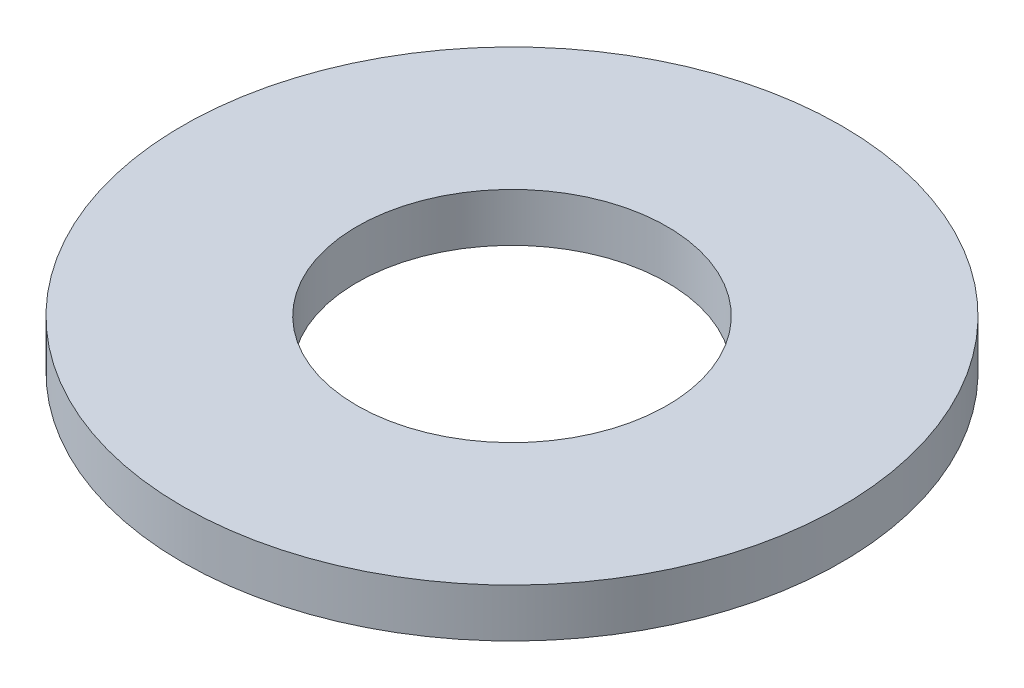
SolidWorks part; units mm, degrees
material "Cast Alloy Steel"
ref_plane "Front" through (0, 0, 0) normal (0, 0, 1) x (1, 0, 0)
ref_plane "Top" through (0, 0, 0) normal (0, 1, 0) x (1, 0, 0)
ref_plane "Right" through (0, 0, 0) normal (1, 0, 0) x (0, 0, -1)
sketch "Sketch1" plane through (0, 0, 0) normal (0, 1, 0) x (1, 0, 0)
  circle A0 centre (0, 0) radius 1.6
  circle A1 centre (0, 0) radius 3.4
  dimension "D1" = 3.2
  dimension "D2" = 6.8
extrude "Extrude1" add sketch "Sketch1" along normal blind 0.5
